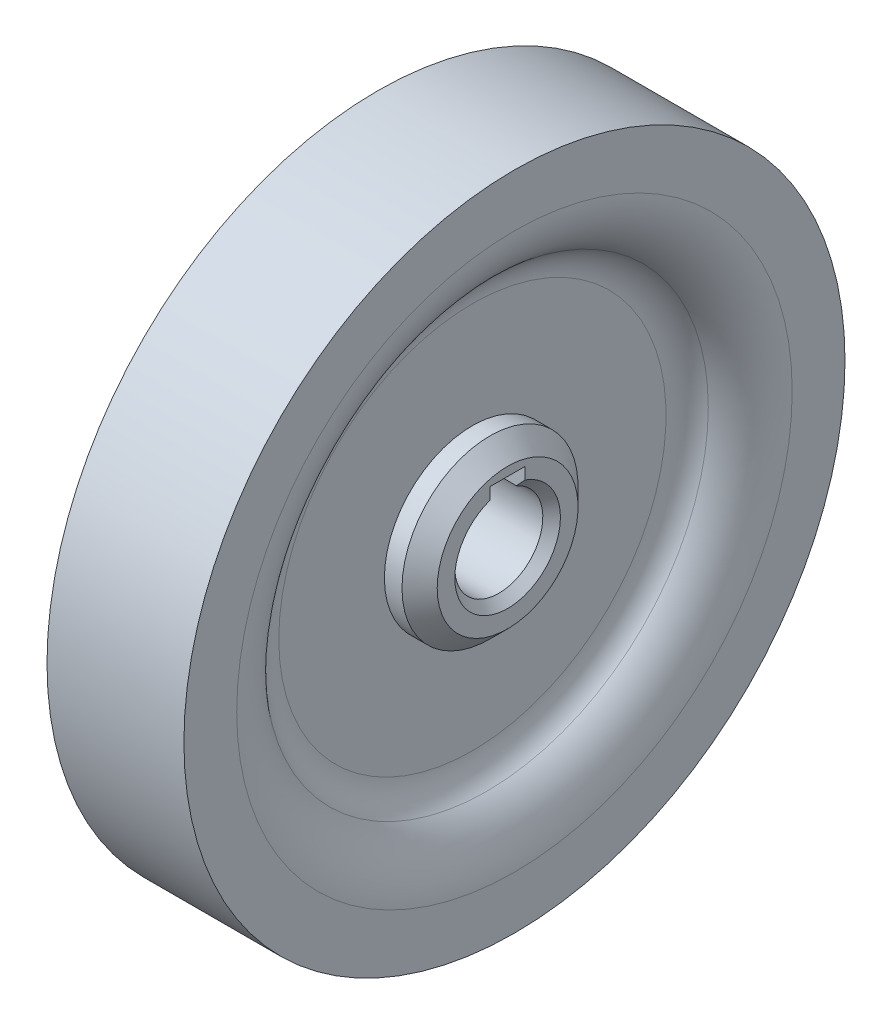
SolidWorks part; units mm, degrees
ref_plane "Płaszczyzna przednia" through (0, 0, 0) normal (0, 0, 1) x (1, 0, 0)
ref_plane "Płaszczyzna górna" through (0, 0, 0) normal (0, 1, 0) x (1, 0, 0)
ref_plane "Płaszczyzna prawa" through (0, 0, 0) normal (1, 0, 0) x (0, 0, -1)
sketch "Szkic1" plane through (0, 0, 0) normal (0, 0, 1) x (1, 0, 0)
  line L0 (-7.7775, 37.5551) -> (-7.7775, 31.5551)
  line L1 (-3, 22) -> (-3, 10)
  line L2 (-3, 10) -> (-7, 10)
  line L3 (-7, 10) -> (-7, 0)
  line L4 (8.5553, 0) -> (-8.5553, 0) construction
  line L5 (0, -20.6553) -> (0, 20.6553) construction
  line L6 (-7.7775, 37.5551) -> (7.7775, 37.5551)
  line L7 (7, 10) -> (7, 0)
  line L8 (3, 10) -> (7, 10)
  line L9 (3, 22) -> (3, 10)
  line L10 (7.7775, 37.5551) -> (7.7775, 31.5551)
  line L11 (-1.7734, 0) -> (7, 0) construction
  line L12 (-7, 0) -> (7, 0)
  arc A0 (-7.7775, 31.5551) -> (-4.6, 25.2) centre (0.1663, 31.5551) ccw
  arc A1 (-4.6, 25.2) -> (-3, 22) centre (-7, 22) cw
  arc A2 (4.6, 25.2) -> (3, 22) centre (7, 22) ccw
  arc A3 (7.7775, 31.5551) -> (4.6, 25.2) centre (-0.1663, 31.5551) cw
  point P6 (-7, 5)
  point P22 (0, 37.5551)
  dimension "D1" = 10
  dimension "D2" = 4
  dimension "D3" = 12
  dimension "D4" = 6
  dimension "D5" = 7
revolve "Obrót1" add sketch "Szkic1" angle 360 about L11
chamfer "Sfazowanie1" distance 2 angle 45 1 edges at (7, 0, 10)
chamfer "Sfazowanie2" distance 2 angle 45 1 edges at (-7, 0, 10)
hole_wizard "Otwór Ø10.0 (10)1" positions "Szkic2" profile "Szkic3" hole size "Ø10.0" standard "ISO" end condition through all
sketch "Szkic2" plane through (-7, 0, 0) normal (-1, 0, 0) x (0, 0, 1)
  point P0 (0, 0)
sketch "Szkic3" plane through (-7, 0, 0) normal (0, 1, 0) x (0, 0, 1)
  line L0 (0, 0) -> (0, 14.7775)
  line L1 (0, 14.7775) -> (5, 14.7775)
  line L2 (5, 14.7775) -> (5, 0)
  line L5 (5, 0) -> (0, 0)
  line L11 (0, -6.35) -> (0, 107.95) construction
  dimension "Średnica otworu na wylot" = 10
  dimension "Głębokość otworu na wylot" = 14.7775
chamfer "Sfazowanie3" distance 1 angle 45 2 edges at (7, 0, 5) (-7, 0, 5)
sketch "Szkic4" plane through (7, 0, 0) normal (1, 0, 0) x (0, 0, -1)
  line L5 (0, 8.5553) -> (0, -8.5553) construction
  line L6 (-2, 7) -> (2, 7)
  line L7 (-2, 7) -> (-2, 3)
  line L8 (-2, 3) -> (2, 3)
  line L9 (2, 7) -> (2, 3)
  line L10 (8.5553, 0) -> (-8.5553, 0) construction
  dimension "D1" = 4
  dimension "D2" = 4
  dimension "D3" = 2
  dimension "D4" = 3
extrude "Wytnij-wyciągnięcie1" cut sketch "Szkic4" against normal through all
